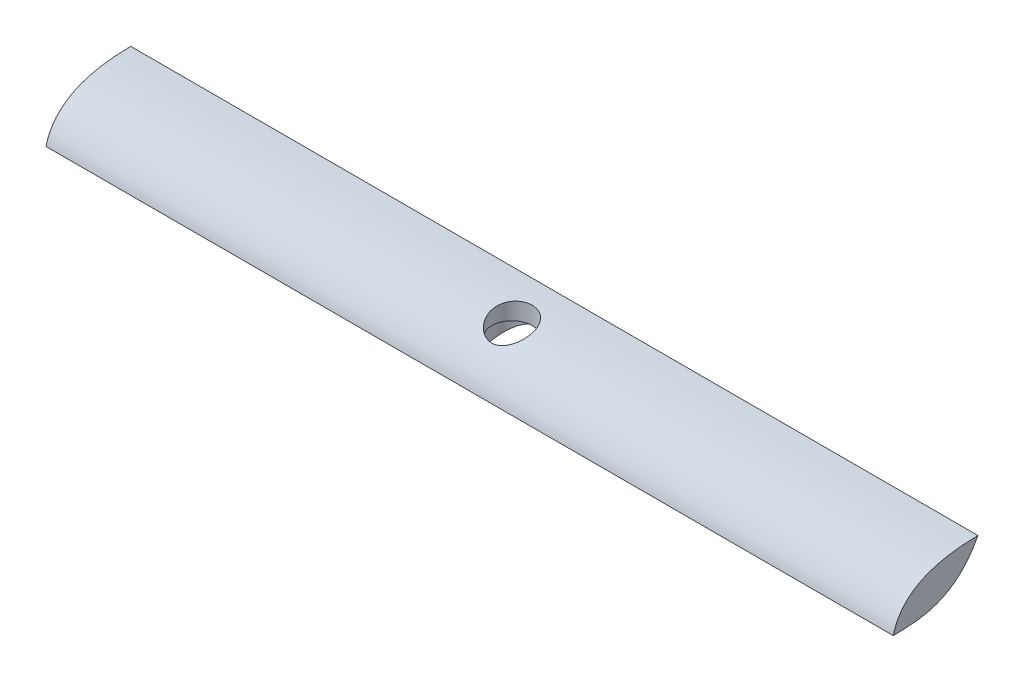
SolidWorks part; units mm, degrees
ref_plane "Plan de face" through (0, 0, 0) normal (0, 0, 1) x (1, 0, 0)
ref_plane "Plan de dessus" through (0, 0, 0) normal (0, 1, 0) x (1, 0, 0)
ref_plane "Plan de droite" through (0, 0, 0) normal (1, 0, 0) x (0, 0, -1)
sketch "Esquisse1" plane through (0, 0, 0) normal (0, 1, 0) x (1, 0, 0)
  circle A0 centre (0, 0) radius 6
extrude "Boss.-Extru.1" add sketch "Esquisse1" along normal blind 6.8
sketch "Esquisse4" plane through (0, 6.8, 0) normal (0, 1, 0) x (-1, 0, 0)
  line L1 (65, -6.5) -> (-65, -6.5)
  line L2 (65, -6.5) -> (65, 6.5)
  line L3 (65, 6.5) -> (-65, 6.5)
  line L4 (-65, -6.5) -> (-65, 6.5)
  circle A0 centre (0, 0) radius 6 construction
  dimension "D1" = 130
  dimension "D2" = 13
  dimension "D3" = 65
  dimension "D4" = 6.5
extrude "Boss.-Extru.4" add sketch "Esquisse4" against normal blind 6.8
sketch "Esquisse2" plane through (0, 6.8, 0) normal (0, 1, 0) x (-1, 0, 0)
  circle A0 centre (0, 0) radius 3.1
  dimension "D1" = 6.2
extrude "Enlèv. mat.-Extru.1" cut sketch "Esquisse2" against normal blind 3.9
sketch "Esquisse3" plane through (0, 0, 0) normal (0, -1, 0) x (1, 0, 0)
  circle A0 centre (0, 0) radius 4
extrude "Enlèv. mat.-Extru.2" cut sketch "Esquisse3" against normal blind 3.9
sketch "Esquisse5" plane through (-65, 0, 0) normal (-1, 0, 0) x (0, 0, 1)
  line L0 (-6.5, 6.8) -> (6.5, 6.8) construction
  spline S0 degree 2 poles (-6.5, 6.8) (6.5825, 6.7376) (6.7981, -2.2975) knots 0 0 0 1 1 1
  spline S1 degree 3 poles (-6.5, 6.8) (-2.7312, -0.2999) (2.8565, 0.0014) (8.3698, 0) knots 0 0 0 0 1 1 1 1
  line M1 (6.5, 6.8) -> (-6.5, 6.8)
  line M2 (-6.5, 6.8) -> (-6.5, 0)
  line M3 (-6.5, 0) -> (6.5, 0)
  line M4 (6.5, 0) -> (6.5, 6.8)
extrude "Enlèv. mat.-Extru.3" cut sketch "Esquisse5" against normal blind 150 contours S1 M2 M3 | S0 M1 M4
